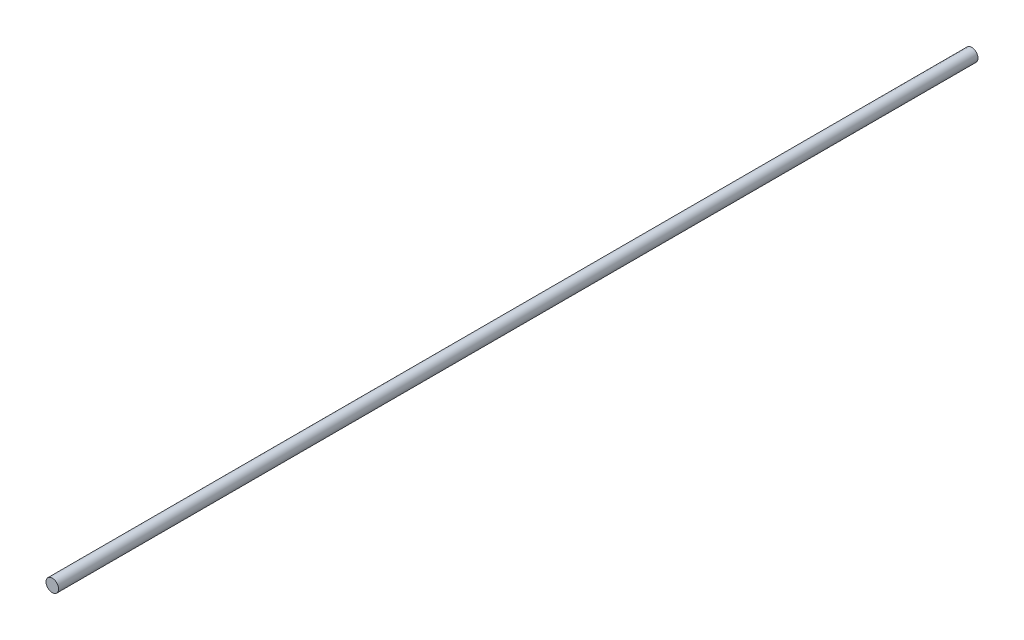
SolidWorks part; units mm, degrees
ref_plane "Front Plane" through (0, 0, 0) normal (0, 0, 1) x (1, 0, 0)
ref_plane "Top Plane" through (0, 0, 0) normal (0, 1, 0) x (1, 0, 0)
ref_plane "Right Plane" through (0, 0, 0) normal (1, 0, 0) x (0, 0, -1)
sketch "Sketch1" plane through (0, 0, 0) normal (0, 0, 1) x (1, 0, 0)
  circle A0 centre (0, 0) radius 1.25
  dimension "D1" = 2.5
extrude "Boss-Extrude1" add sketch "Sketch1" along normal blind 182.2
